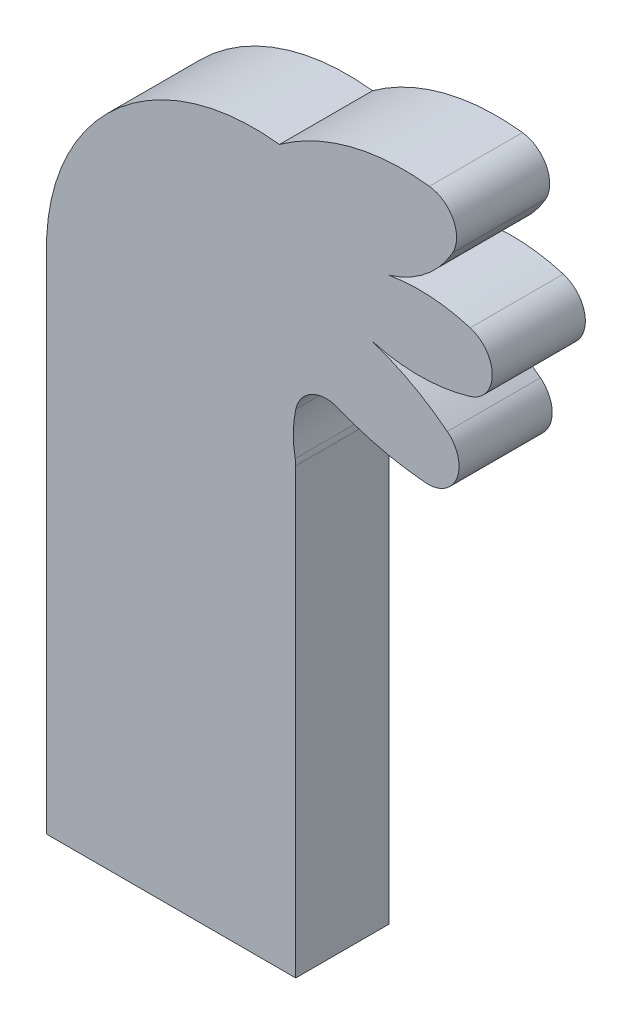
SolidWorks part; units mm, degrees
ref_plane "Alzado" through (0, 0, 0) normal (0, 0, 1) x (1, 0, 0)
ref_plane "Planta" through (0, 0, 0) normal (0, 1, 0) x (1, 0, 0)
ref_plane "Vista lateral" through (0, 0, 0) normal (1, 0, 0) x (0, 0, -1)
sketch "Model" plane through (0, 0, 0) normal (0, 0, 1) x (1, 0, 0)
  line L0 (9.7405, -46.1017) -> (9.7405, -31.8033)
  line L1 (1.7145, -46.1017) -> (9.7405, -46.1017)
  line L2 (1.7145, -29.4352) -> (1.7145, -46.1017)
  arc A0 (15.3632, -27.0589) -> (15.3632, -25.1444) centre (15.074, -26.1017) ccw
  arc A1 (12.2145, -27.1017) -> (15.3632, -27.0589) centre (13.7145, -21.6017) ccw
  arc A2 (14.6256, -28.4064) -> (12.2145, -27.1017) centre (9.7145, -34.6017) ccw
  arc A3 (13.922, -30.1867) -> (14.6256, -28.4064) centre (14.0044, -29.1901) ccw
  arc A4 (11.0959, -29.5127) -> (13.922, -30.1867) centre (14.7145, -20.6017) ccw
  arc A5 (11.0959, -29.5127) -> (9.7438, -30.2209) centre (10.7197, -30.4392) ccw
  arc A6 (12.7439, -24.984) -> (14.7961, -23.3347) centre (11.7145, -21.6017) ccw
  arc A7 (9.7438, -30.2209) -> (9.7226, -31.6148) centre (13.088, -30.9688) ccw
  arc A8 (9.7405, -31.8033) -> (9.7226, -31.6148) centre (8.7405, -31.8033) ccw
  arc A9 (15.3632, -25.1444) -> (12.7439, -24.984) centre (13.7145, -30.6017) ccw
  arc A10 (9.2145, -23.1017) -> (1.7145, -29.4352) centre (8.395, -29.7387) ccw
  arc A11 (14.0469, -21.8521) -> (9.2145, -23.1017) centre (13.2145, -28.6017) ccw
  arc A12 (14.7961, -23.3347) -> (14.0469, -21.8521) centre (13.9245, -22.8446) ccw
extrude "Saliente-Extruir1" add sketch "Model" along normal blind 3
